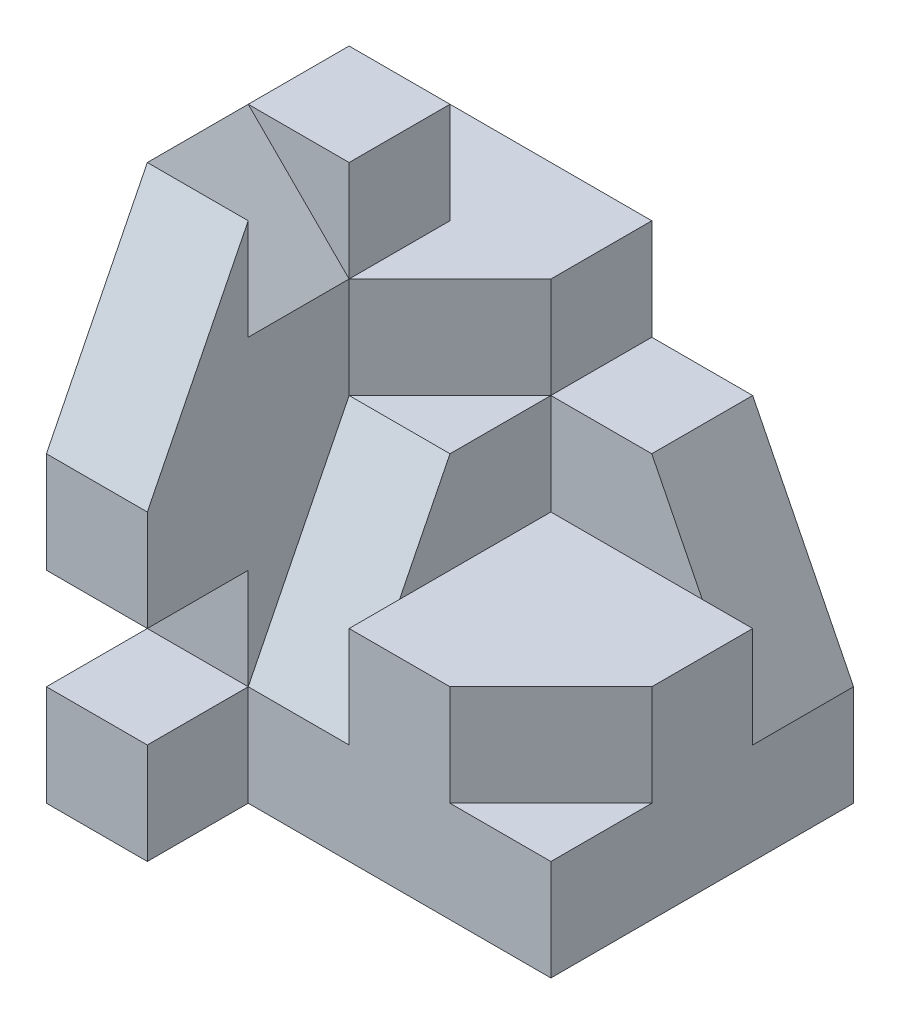
SolidWorks part; units mm, degrees
ref_plane "Front Plane" through (0, 0, 0) normal (0, 0, 1) x (1, 0, 0)
ref_plane "Top Plane" through (0, 0, 0) normal (0, 1, 0) x (1, 0, 0)
ref_plane "Right Plane" through (0, 0, 0) normal (1, 0, 0) x (0, 0, -1)
sketch "Sketch1" plane through (0, 0, 0) normal (0, 0, 1) x (1, 0, 0)
  line L1 (2, -2.5) -> (-2, -2.5)
  line L2 (2, -2.5) -> (2, 2.5)
  line L3 (2, 2.5) -> (-2, 2.5)
  line L4 (-2, -2.5) -> (-2, 2.5)
  line L5 (2, -2.5) -> (-2, 2.5) construction
  line L6 (2, 2.5) -> (-2, -2.5) construction
  point P0 (0, 0)
  dimension "D1" = 5
  dimension "D2" = 4
extrude "Boss-Extrude1" add sketch "Sketch1" along normal blind 4
sketch "Sketch2" plane through (0, 2.5, 0) normal (0, 1, 0) x (1, 0, 0)
  line L0 (2, -4) -> (2, -3)
  line L1 (2, -4) -> (2, 0) construction
  line L2 (2, -3) -> (-1, -3)
  line L3 (-1, -3) -> (-1, -4)
  line L4 (2, -4) -> (-2, -4) construction
  line L5 (-1, -4) -> (2, -4)
  dimension "D1" = 1
  dimension "D2" = 3
extrude "Cut-Extrude1" cut sketch "Sketch2" against normal through all
sketch "Sketch3" plane through (-1, 0, 0) normal (1, 0, 0) x (0, 0, -1)
  line L0 (-4, -1.5) -> (-3, -1.5)
  line L1 (-4, -2.5) -> (-4, 2.5) construction
  line L2 (-3, -2.5) -> (-3, 2.5) construction
  line L3 (-3, -1.5) -> (-3, -0.5)
  line L4 (-3, -0.5) -> (-4, -0.5)
  line L5 (-4, -0.5) -> (-4, -1.5)
  line L6 (-3, -2.5) -> (-4, -2.5) construction
  dimension "D1" = 1
  dimension "D2" = 1
extrude "Cut-Extrude2" cut sketch "Sketch3" against normal blind 1
sketch "Sketch4" plane through (-1, 0, 0) normal (1, 0, 0) x (0, 0, -1)
  line L0 (-3, 2.5) -> (-4, 0.5)
  line L1 (-4, -0.5) -> (-4, 2.5) construction
  line L2 (-4, 0.5) -> (-4, 2.5)
  line L3 (-4, 2.5) -> (-3, 2.5)
  line L4 (-3, -0.5) -> (-4, -0.5) construction
  dimension "D1" = 1
extrude "Cut-Extrude3" cut sketch "Sketch4" against normal blind 1
sketch "Sketch5" plane through (0, 2.5, 0) normal (0, 1, 0) x (1, 0, 0)
  line L0 (-2, 0) -> (-2, -1)
  line L1 (-2, -3) -> (-2, 0) construction
  line L2 (-2, -1) -> (-1, -1)
  line L3 (-1, -1) -> (-1, -3)
  line L4 (-1, -3) -> (2, -3)
  line L5 (2, -3) -> (2, 0)
  line L6 (2, 0) -> (-2, 0)
  dimension "D1" = 1
extrude "Cut-Extrude5" cut sketch "Sketch5" against normal blind 1
sketch "Sketch6" plane through (0, 1.5, 0) normal (0, 1, 0) x (1, 0, 0)
  line L0 (2, -3) -> (2, -1)
  line L1 (2, -3) -> (2, 0) construction
  line L2 (2, -1) -> (0, -1)
  line L3 (0, -1) -> (0, -3)
  line L4 (-1, -3) -> (2, -3) construction
  line L5 (0, -3) -> (2, -3)
  dimension "D1" = 2
  dimension "D2" = 2
extrude "Cut-Extrude6" cut sketch "Sketch6" against normal blind 2
sketch "Sketch7" plane through (0, -0.5, 0) normal (0, 1, 0) x (1, 0, 0)
  line L0 (2, -3) -> (2, -2)
  line L1 (2, -3) -> (2, -1) construction
  line L2 (2, -2) -> (1, -3)
  line L3 (0, -3) -> (2, -3) construction
  line L4 (1, -3) -> (2, -3)
  dimension "D1" = 1
  dimension "D2" = 1
extrude "Cut-Extrude7" cut sketch "Sketch7" against normal blind 1
sketch "Sketch8" plane through (0, 0, 0) normal (0, 0, -1) x (-1, 0, 0)
  line L0 (-2, -1.5) -> (-2, 1.5)
  line L1 (-2, -2.5) -> (-2, 1.5) construction
  line L2 (-2, 1.5) -> (0, 1.5)
  line L3 (-2, 1.5) -> (2, 1.5) construction
  line L4 (0, 1.5) -> (0, 0.5)
  line L5 (0, 0.5) -> (-1, 0.5)
  line L6 (-1, 0.5) -> (-2, -1.5)
  dimension "D1" = 2
  dimension "D2" = 1
  dimension "D3" = 1
  dimension "D4" = 1
extrude "Cut-Extrude8" cut sketch "Sketch8" against normal blind 1
sketch "Sketch9" plane through (0, 1.5, 0) normal (0, 1, 0) x (1, 0, 0)
  line L0 (0, -1) -> (-1, -2)
  line L1 (-1, -1) -> (-1, -3) construction
  line L2 (-1, -2) -> (-1, -3)
  line L3 (-1, -3) -> (0, -3)
  line L4 (0, -3) -> (0, -1)
extrude "Cut-Extrude9" cut sketch "Sketch9" against normal blind 1
sketch "Sketch10" plane through (0, 0, 3) normal (0, 0, 1) x (1, 0, 0)
  line L0 (-1, -1.5) -> (0, -1.5)
  dimension "D1" = 1
sketch "Sketch11" plane through (0, 0.5, 0) normal (0, 1, 0) x (1, 0, 0)
  line L0 (-1, -2) -> (0, -2)
  line L1 (0, -3) -> (0, -1) construction
ref_plane "Plane1" through (0, 0.9, 1.8) normal (0, 0.4472, 0.8944) x (1, 0, 0)
sketch "Sketch12" plane through (0, 0.9, 1.8) normal (0, 0.4472, 0.8944) x (1, 0, 0)
  line L0 (0, -0.4472) -> (0, -2.6833)
  line L1 (0, -2.6833) -> (-1, -2.6833)
  line L2 (-1, -2.6833) -> (-1, -0.4472)
  line L3 (-1, -0.4472) -> (0, -0.4472)
extrude "Cut-Extrude10" cut sketch "Sketch12" along normal blind 1
sketch "Sketch13" plane through (-1, 0, 0) normal (1, 0, 0) x (0, 0, -1)
  line L0 (-2, 1.5) -> (-3, 1.5)
  dimension "D1" = 1
ref_plane "Plane2" through (0.25, 0.25, 0) normal (-0.7071, -0.7071, 0) x (0, 0, 1)
sketch "Sketch14" plane through (0.25, 0.25, 0) normal (-0.7071, -0.7071, 0) x (0, 0, 1)
  line L0 (2, 1.7678) -> (3, 1.7678)
  line L1 (3, 1.7678) -> (3, 3.182)
  line L2 (3, 3.182) -> (2, 3.182)
  line L3 (3, 3.182) -> (1, 3.182) construction
  line L4 (2, 3.182) -> (2, 1.7678)
extrude "Cut-Extrude11" cut sketch "Sketch14" against normal blind 1
